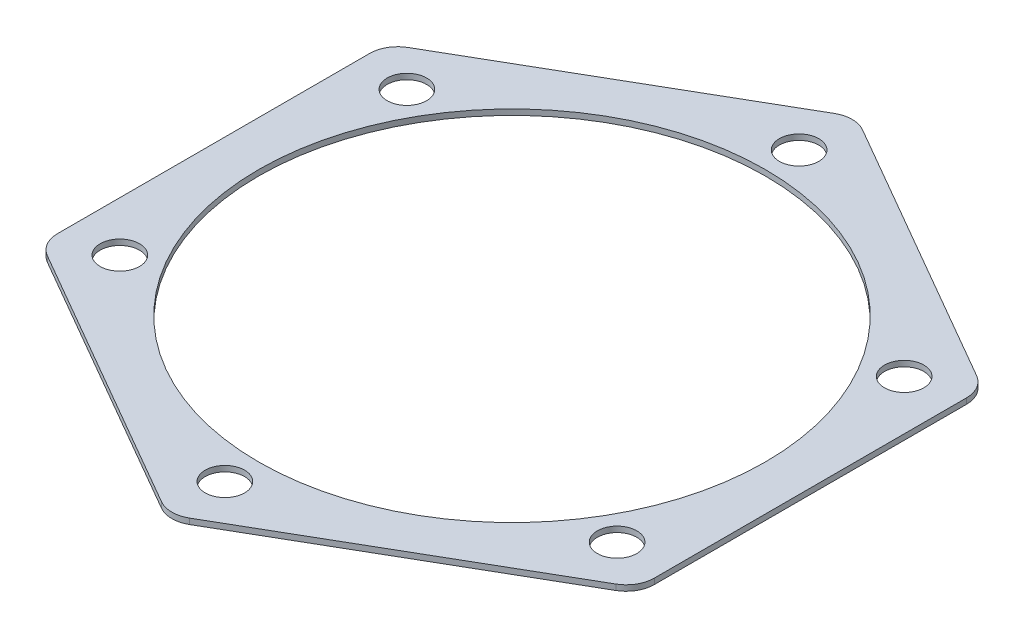
SolidWorks part; units mm, degrees
material "BUTYL"
ref_plane "Front Plane" through (0, 0, 0) normal (0, 0, 1) x (1, 0, 0)
ref_plane "Top Plane" through (0, 0, 0) normal (0, 1, 0) x (1, 0, 0)
ref_plane "Right Plane" through (0, 0, 0) normal (1, 0, 0) x (0, 0, -1)
sketch "Sketch2" plane through (0, 0, 0) normal (0, 1, 0) x (1, 0, 0)
  line L1 (-2.5, 59.7558) -> (-50.5, 32.0429)
  line L2 (-53, 27.7128) -> (-53, -27.7128)
  line L3 (-50.5, -32.0429) -> (-2.5, -59.7558)
  line L4 (2.5, -59.7558) -> (50.5, -32.0429)
  line L5 (53, -27.7128) -> (53, 27.7128)
  line L6 (50.5, 32.0429) -> (2.5, 59.7558)
  circle A0 centre (0, 0) radius 45
  circle A2 centre (0, 0) radius 53 construction
  arc A4 (-2.5, 59.7558) -> (2.5, 59.7558) centre (0, 55.4256) cw
  arc A5 (50.5, 32.0429) -> (53, 27.7128) centre (48, 27.7128) cw
  arc A6 (53, -27.7128) -> (50.5, -32.0429) centre (48, -27.7128) cw
  arc A7 (-2.5, -59.7558) -> (2.5, -59.7558) centre (0, -55.4256) ccw
  arc A8 (-50.5, -32.0429) -> (-53, -27.7128) centre (-48, -27.7128) cw
  arc A9 (-53, 27.7128) -> (-50.5, 32.0429) centre (-48, 27.7128) cw
  point P13 (0, 61.1991)
  point P24 (-53, 30.5996)
  dimension "D1" = 90
  dimension "D2" = 106
  dimension "D5" = 5
  dimension "D4" = 53
extrude "Boss-Extrude1" add sketch "Sketch2" along normal blind 1
sketch "Sketch3" plane through (0, 1, 0) normal (0, 1, 0) x (1, 0, 0)
  circle A1 centre (0, 51) radius 3.5
  dimension "D2" = 7
extrude "Cut-Extrude1" cut sketch "Sketch3" against normal blind 1
pattern_circular "CirPattern1" count 6 over 360 about axis through (0, 0, 0) along (0, 1, 0) of "Cut-Extrude1"
